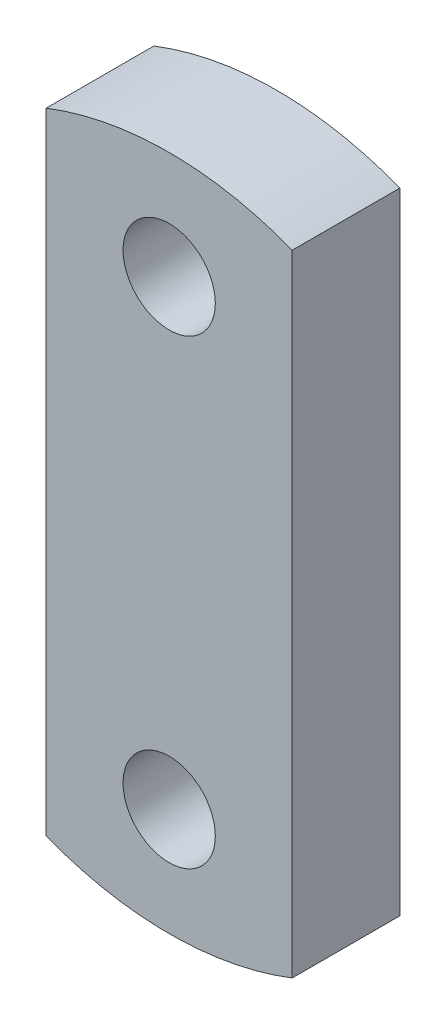
SolidWorks part; units mm, degrees
ref_plane "Front Plane" through (0, 0, 0) normal (0, 0, 1) x (1, 0, 0)
ref_plane "Top Plane" through (0, 0, 0) normal (0, 1, 0) x (1, 0, 0)
ref_plane "Right Plane" through (0, 0, 0) normal (1, 0, 0) x (0, 0, -1)
sketch "Sketch1" plane through (0, 0, 0) normal (0, 0, 1) x (1, 0, 0)
  line L0 (-40, 102.4695) -> (-40, -102.4695)
  line L5 (40, -102.4695) -> (40, 102.4695)
  line L6 (0, 132.5291) -> (0, -168.9214) construction
  line L7 (-130.3792, 0) -> (122.8732, 0) construction
  arc A0 (-40, -102.4695) -> (40, -102.4695) centre (0, 0) ccw
  circle A1 centre (0, 75) radius 15
  circle A2 centre (0, -75) radius 15
  arc A3 (40, 102.4695) -> (-40, 102.4695) centre (0, 0) ccw
  point P14 (0, 0)
  dimension "D1" = 220
  dimension "D2" = 150
  dimension "D3" = 30
  dimension "D4" = 80
extrude "Boss-Extrude1" add sketch "Sketch1" along normal blind 35
